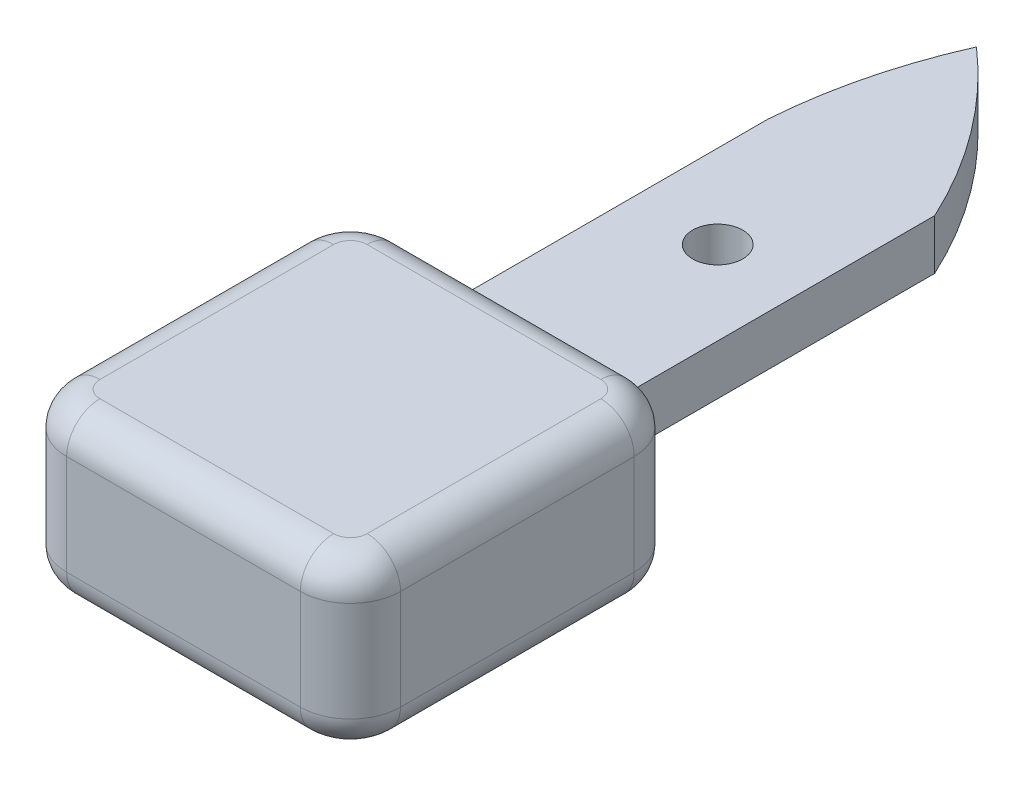
SolidWorks part; units mm, degrees
ref_plane "Front Plane" through (0, 0, 0) normal (0, 0, 1) x (1, 0, 0)
ref_plane "Top Plane" through (0, 0, 0) normal (0, 1, 0) x (1, 0, 0)
ref_plane "Right Plane" through (0, 0, 0) normal (1, 0, 0) x (0, 0, -1)
sketch "Sketch1" plane through (0, 0, 0) normal (0, 1, 0) x (1, 0, 0)
  line L0 (0, 0) -> (0, 20)
  line L1 (10, 20) -> (10, 0)
  line L2 (0, 0) -> (-2, 0)
  line L3 (-5, -3) -> (-5, -17)
  line L4 (-2, -20) -> (12, -20)
  line L5 (15, -17) -> (15, -3)
  line L6 (12, 0) -> (10, 0)
  arc A0 (0, 20) -> (2.5, 30) centre (29.9216, 17.8321) cw
  arc A1 (2.5, 30) -> (10, 20) centre (-17.2234, 7.395) cw
  arc A2 (-2, 0) -> (-5, -3) centre (-2, -3) ccw
  arc A3 (15, -3) -> (12, 0) centre (12, -3) ccw
  arc A4 (12, -20) -> (15, -17) centre (12, -17) ccw
  arc A5 (-5, -17) -> (-2, -20) centre (-2, -17) ccw
  circle A6 centre (5, 12) radius 1.5
  point P15 (-5, 0)
  point P18 (15, 0)
  point P23 (-5, -20)
  dimension "D3" = 30
  dimension "D4" = 30
  dimension "D11" = 3
  dimension "D12" = 3
  dimension "D1" = 20
  dimension "D2" = 20
  dimension "D5" = 10
  dimension "D6" = 10
  dimension "D7" = 2.5
  dimension "D8" = 5
  dimension "D9" = 5
  dimension "D10" = 20
  dimension "D13" = 12
  dimension "D14" = 5
extrude "Boss-Extrude1" add sketch "Sketch1" along normal blind 3
ref_plane "Plane1" through (0, 1.5, 0) normal (0, 1, 0) x (1, 0, 0)
sketch "Sketch2" plane through (0, 1.5, 0) normal (0, 1, 0) x (1, 0, 0)
  line L0 (0, 0) -> (-2, 0) construction
  line L1 (12, 0) -> (10, 0) construction
  line L2 (15, -17) -> (15, -3) construction
  line L3 (-2, -20) -> (12, -20) construction
  line L4 (-5, -3) -> (-5, -17) construction
  line L5 (0, 0) -> (-2, 0)
  line L6 (12, 0) -> (10, 0)
  line L7 (15, -17) -> (15, -3)
  line L8 (-2, -20) -> (12, -20)
  line L9 (-5, -3) -> (-5, -17)
  line L10 (0, 0) -> (10, 0)
  arc A0 (15, -3) -> (12, 0) centre (12, -3) ccw construction
  arc A1 (12, -20) -> (15, -17) centre (12, -17) ccw construction
  arc A2 (-5, -17) -> (-2, -20) centre (-2, -17) ccw construction
  arc A3 (-2, 0) -> (-5, -3) centre (-2, -3) ccw construction
  arc A4 (15, -3) -> (12, 0) centre (12, -3) ccw
  arc A5 (12, -20) -> (15, -17) centre (12, -17) ccw
  arc A6 (-5, -17) -> (-2, -20) centre (-2, -17) ccw
  arc A7 (-2, 0) -> (-5, -3) centre (-2, -3) ccw
extrude "Boss-Extrude2" add sketch "Sketch2" along normal mid plane 10
fillet "Fillet1" radius 2 16 edges at (-4.1213, -3.5, 0.8787) (5, -3.5, 0) (14.1213, -3.5, 0.8787) (15, -3.5, 10) (14.1213, -3.5, 19.1213) (-4.1213, -3.5, 19.1213) (-4.1213, 6.5, 0.8787) (5, 6.5, 0) (14.1213, 6.5, 0.8787) (15, 6.5, 10) (14.1213, 6.5, 19.1213) (-4.1213, 6.5, 19.1213) (5, 6.5, 20) (5, -3.5, 20) (-5, -3.5, 10) (-5, 6.5, 10)
